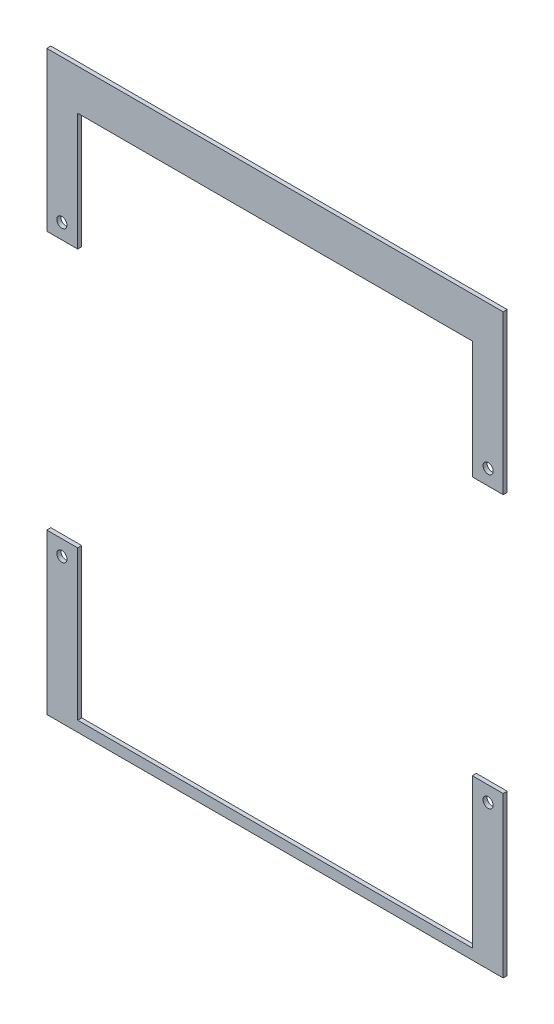
SolidWorks part; units mm, degrees
material "Neoprene Foam"
ref_plane "Front Plane" through (0, 0, 0) normal (0, 0, 1) x (1, 0, 0)
ref_plane "Top Plane" through (0, 0, 0) normal (0, 1, 0) x (1, 0, 0)
ref_plane "Right Plane" through (0, 0, 0) normal (1, 0, 0) x (0, 0, -1)
sketch "Sketch1" plane through (0, 0, 0) normal (0, 0, 1) x (1, 0, 0)
  line L0 (0, -107.38) -> (0, 119.25)
  line L1 (-77.5, 103.25) -> (77.5, 103.25)
  line L2 (-77.5, 103.25) -> (-77.5, -103.25)
  line L3 (-77.5, -103.25) -> (77.5, -103.25)
  line L4 (77.5, 103.25) -> (77.5, -103.25) construction
  line L5 (-77.5, 103.25) -> (77.5, -103.25) construction
  line L6 (-77.5, -103.25) -> (77.5, 103.25) construction
  line L7 (-89.6514, 119.25) -> (89.6514, 119.25)
  line L8 (-89.6514, 119.25) -> (-89.6514, -107.38)
  line L9 (-89.6514, -107.38) -> (89.6514, -107.38)
  line L10 (89.6514, 119.25) -> (89.6514, -107.38) construction
  line L11 (-83.72, 63.03) -> (-83.72, -50.6224) construction
  line L12 (-89.6514, 57.03) -> (-77.5, 57.03)
  line L13 (-89.6514, -44.6224) -> (-77.5, -44.6224)
  circle A0 centre (-83.72, 63.03) radius 2
  circle A1 centre (-83.72, -50.6224) radius 2
  point P0 (0, 0)
  point P6 (0, 0)
  dimension "D6" = 4
  dimension "D7" = 4
  dimension "D12" = 6
  dimension "D1" = 155
  dimension "D2" = 206.5
  dimension "D3" = 179.3028
  dimension "D4" = 4.13
  dimension "D5" = 16
  dimension "D8" = 5.9314
  dimension "D9" = 56.7576
  dimension "D10" = 170.41
  dimension "D11" = 6
extrude "Repeating Frame" add sketch "Sketch1" along normal blind 1.5875 contours L8 L12 L2 L1 L0 L7 A0 | L13 L8 L9 L0 L3 L2 A1
mirror "Mirror1" about plane through (0, 0, 0) normal (1, 0, 0) of "Repeating Frame"
